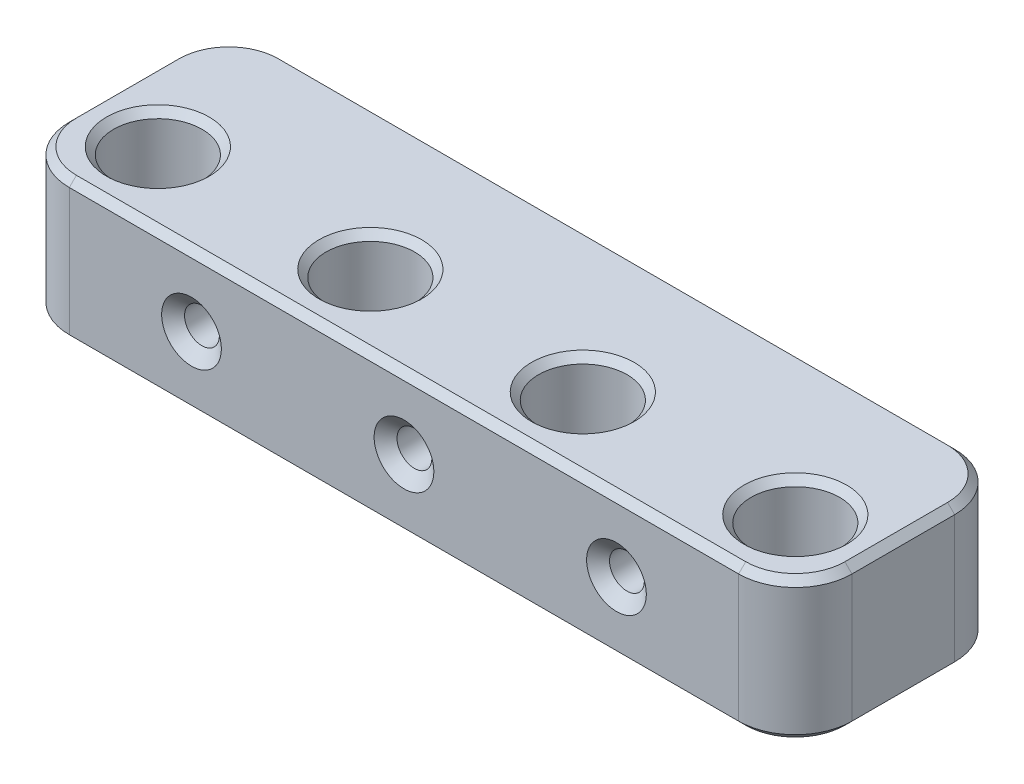
SolidWorks part; units mm, degrees
ref_plane "Front Plane" through (0, 0, 0) normal (0, 0, 1) x (1, 0, 0)
ref_plane "Top Plane" through (0, 0, 0) normal (0, 1, 0) x (1, 0, 0)
ref_plane "Right Plane" through (0, 0, 0) normal (1, 0, 0) x (0, 0, -1)
sketch "Sketch1" plane through (0, 0, 0) normal (0, 1, 0) x (1, 0, 0)
  line L1 (-10.25, -10.25) -> (10.25, -10.25)
  line L2 (-10.25, -10.25) -> (-10.25, 10.25)
  line L3 (-10.25, 10.25) -> (10.25, 10.25)
  line L4 (10.25, -10.25) -> (10.25, 10.25)
  line L5 (-10.25, -10.25) -> (10.25, 10.25) construction
  line L6 (-10.25, 10.25) -> (10.25, -10.25) construction
  circle A0 centre (0, 0) radius 6.25
  circle A1 centre (0, 0) radius 10.25 construction
  dimension "D1" = 12.5
  dimension "D2" = 4
extrude "Boss-Extrude1" add sketch "Sketch1" along normal blind 20
sketch "Sketch2" plane through (0, 0, -10.25) normal (0, 0, -1) x (-1, 0, 0)
  line L4 (-10.25, 0) -> (10.25, 0)
  line L5 (10.25, 0) -> (10.25, 20)
  line L6 (10.25, 20) -> (-10.25, 20)
  line L7 (-10.25, 20) -> (-10.25, 0)
  line L8 (-10.25, 0) -> (10.25, 0)
  line L9 (10.25, 0) -> (10.25, 20)
  line L10 (10.25, 20) -> (-10.25, 20)
  line L11 (-10.25, 20) -> (-10.25, 0)
  dimension "D1" = 0
extrude "Boss-Extrude2" add sketch "Sketch2" along normal blind 10
pattern_linear "LPattern1" count 4 spacing 30 along (1, 0, 0) of "Boss-Extrude1"
sketch "Sketch3" plane through (0, 20, 0) normal (0, 1, 0) x (1, 0, 0)
  line L1 (10.25, 20.25) -> (19.75, 20.25)
  line L2 (10.25, 20.25) -> (10.25, -10.25)
  line L3 (10.25, -10.25) -> (19.75, -10.25)
  line L4 (19.75, 20.25) -> (19.75, -10.25)
  line L5 (40.25, 20.25) -> (49.75, 20.25)
  line L6 (40.25, 20.25) -> (40.25, -10.25)
  line L7 (40.25, -10.25) -> (49.75, -10.25)
  line L8 (49.75, 20.25) -> (49.75, -10.25)
  line L9 (70.25, 20.25) -> (79.75, 20.25)
  line L10 (70.25, 20.25) -> (70.25, -10.25)
  line L11 (70.25, -10.25) -> (79.75, -10.25)
  line L12 (79.75, 20.25) -> (79.75, -10.25)
extrude "Boss-Extrude3" add sketch "Sketch3" against normal up to vertex (20 mm away)
sketch "Sketch4" plane through (0, 20, 0) normal (0, 1, 0) x (1, 0, 0)
  point P0 (0, 0)
  point P1 (30, 0)
  point P3 (60, 0)
  point P5 (90, 0)
sketch "Sketch5" plane through (0, 0, 10.25) normal (0, 0, 1) x (1, 0, 0)
  line L0 (0, 20) -> (30, 20) construction
  line L1 (30, 20) -> (60, 20) construction
  line L2 (60, 20) -> (90, 20) construction
  line L3 (0, 20) -> (30, 0) construction
  line L4 (-10.25, 0) -> (100.25, 0) construction
  line L5 (30, 0) -> (60, 20) construction
  line L6 (60, 20) -> (90, 0) construction
  point P4 (15, 10)
  point P13 (45, 10)
  point P14 (75, 10)
hole_wizard "CSK for #8 Flat Head Machine Screw (100)1" positions "3DSketch1" profile "Sketch6" countersink size "#8" standard "ANSI Inch" end condition through all
sketch3d "3DSketch1"
  line L0 (60, 20, 10.25) -> (90, 0, 10.25) construction
  point P0 (15, 10, 10.25)
  point P3 (45, 10, 10.25)
  point P6 (75, 10, 10.25)
  point P10 (75, 10, 10.25)
  point P13 (75, 10, 10.25)
sketch "Sketch6" plane through (15, 10, 10.25) normal (1, 0, 0) x (0, -1, 0)
  line L0 (0, 0) -> (0, 30.5)
  line L1 (0, 30.5) -> (2.4574, 30.5)
  line L2 (2.4574, 30.5) -> (2.4574, 1.4759)
  line L3 (2.4574, 1.4759) -> (4.2164, 0)
  line L5 (4.2164, 0) -> (0, 0)
  line L6 (-2.4574, 1.4759) -> (-4.2164, 0) construction
  line L11 (0, -6.35) -> (0, 107.95) construction
  dimension "Thru Hole Dia." = 4.9149
  dimension "Thru Hole Depth" = 30.5
  dimension "Near C'Sink Dia." = 8.4328
  dimension "Near C'Sink Angle" = 100
fillet "Fillet1" radius 8 4 edges at (-10.25, 10, -20.25) (100.25, 10, -20.25) (100.25, 10, 10.25) (-10.25, 10, 10.25)
chamfer "Chamfer1" distance 1 angle 45 24 edges at (90, 20, 6.25) (90, 0, 6.25) (60, 20, 6.25) (60, 0, 6.25) (30, 20, 6.25) (30, 0, 6.25) (0, 0, 6.25) (-7.9069, 0, 7.9069) (45, 0, 10.25) (97.9069, 0, 7.9069) (100.25, 0, -5) (100.25, 20, -5) (97.9069, 0, -17.9069) (45, 0, -20.25) (-7.9069, 0, -17.9069) (-10.25, 0, -5) (0, 20, 6.25) (97.9069, 20, -17.9069) (97.9069, 20, 7.9069) (45, 20, 10.25) (-7.9069, 20, 7.9069) (-10.25, 20, -5) (-7.9069, 20, -17.9069) (45, 20, -20.25)
